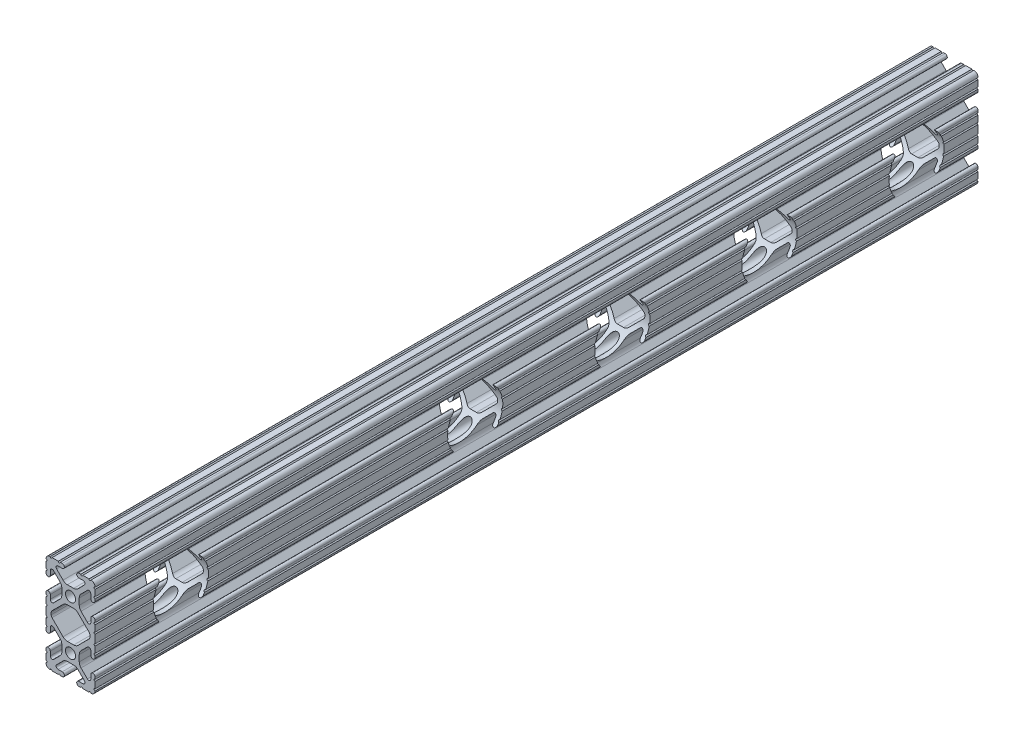
SolidWorks part; units mm, degrees
ref_plane "Front Plane" through (0, 0, 0) normal (0, 0, 1) x (1, 0, 0)
ref_plane "Top Plane" through (0, 0, 0) normal (0, 1, 0) x (1, 0, 0)
ref_plane "Right Plane" through (0, 0, 0) normal (1, 0, 0) x (0, 0, -1)
ref_plane "Plane1" through (0, 0, -889) normal (0, 0, -1) x (-1, 0, 0)
sketch "Sketch1" plane through (0, 0, -889) normal (0, 0, -1) x (-1, 0, 0)
  line L0 (10.033, 13.1521) -> (10.033, 12.2479)
  line L1 (9.5718, 11.1343) -> (3.8759, 5.4384)
  line L2 (1.6308, 4.5085) -> (-1.6308, 4.5085)
  line L3 (-3.8759, 5.4384) -> (-9.5718, 11.1343)
  line L4 (-10.033, 12.2479) -> (-10.033, 13.1521)
  line L5 (-9.5718, 14.2657) -> (-3.8759, 19.9616)
  line L6 (-1.6308, 20.8915) -> (1.6308, 20.8915)
  line L7 (3.8759, 19.9616) -> (9.5718, 14.2657)
  line L8 (9.5504, 38.1) -> (6.3246, 38.1)
  line L9 (5.3086, 38.1) -> (4.3023, 38.1)
  line L10 (4.3023, 35.8902) -> (6.4748, 35.8902)
  line L11 (7.1932, 34.1558) -> (3.8759, 30.8384)
  line L12 (1.6308, 29.9085) -> (-1.6308, 29.9085)
  line L13 (-3.8759, 30.8384) -> (-7.1932, 34.1558)
  line L14 (-6.4748, 35.8902) -> (-4.3023, 35.8902)
  line L15 (-4.3023, 38.1) -> (-5.3086, 38.1)
  line L16 (-6.3246, 38.1) -> (-9.5504, 38.1)
  line L17 (-12.7, 34.9504) -> (-12.7, 31.7246)
  line L18 (-12.7, 30.7086) -> (-12.7, 29.7023)
  line L19 (-10.4902, 29.7023) -> (-10.4902, 31.8748)
  line L20 (-8.7558, 32.5932) -> (-5.4384, 29.2759)
  line L21 (-4.5085, 27.0308) -> (-4.5085, 23.7692)
  line L22 (-5.4384, 21.5241) -> (-8.7558, 18.2068)
  line L23 (-10.4902, 18.9252) -> (-10.4902, 21.0977)
  line L24 (-12.7, 21.0977) -> (-12.7, 20.0914)
  line L25 (-12.7, 19.0754) -> (-12.7, 15.8496)
  line L26 (-12.7, 14.8336) -> (-12.7, 10.5664)
  line L27 (-12.7, 9.5504) -> (-12.7, 6.3246)
  line L28 (-12.7, 5.3086) -> (-12.7, 4.3023)
  line L29 (-10.4902, 4.3023) -> (-10.4902, 6.4748)
  line L30 (-8.7558, 7.1932) -> (-5.4384, 3.8759)
  line L31 (-4.5085, 1.6308) -> (-4.5085, -1.6308)
  line L32 (-5.4384, -3.8759) -> (-8.7558, -7.1932)
  line L33 (-10.4902, -6.4748) -> (-10.4902, -4.3023)
  line L34 (-12.7, -4.3023) -> (-12.7, -5.3086)
  line L35 (-12.7, -6.3246) -> (-12.7, -9.5504)
  line L36 (-9.5504, -12.7) -> (-6.3246, -12.7)
  line L37 (-5.3086, -12.7) -> (-4.3023, -12.7)
  line L38 (-4.3023, -10.4902) -> (-6.4748, -10.4902)
  line L39 (-7.1932, -8.7558) -> (-3.8759, -5.4384)
  line L40 (-1.6308, -4.5085) -> (1.6308, -4.5085)
  line L41 (3.8759, -5.4384) -> (7.1932, -8.7558)
  line L42 (6.4748, -10.4902) -> (4.3023, -10.4902)
  line L43 (4.3023, -12.7) -> (5.3086, -12.7)
  line L44 (6.3246, -12.7) -> (9.5504, -12.7)
  line L45 (12.7, -9.5504) -> (12.7, -6.3246)
  line L46 (12.7, -5.3086) -> (12.7, -4.3023)
  line L47 (10.4902, -4.3023) -> (10.4902, -6.4748)
  line L48 (8.7558, -7.1932) -> (5.4384, -3.8759)
  line L49 (4.5085, -1.6308) -> (4.5085, 1.6308)
  line L50 (5.4384, 3.8759) -> (8.7558, 7.1932)
  line L51 (10.4902, 6.4748) -> (10.4902, 4.3023)
  line L52 (12.7, 4.3023) -> (12.7, 5.3086)
  line L53 (12.7, 6.3246) -> (12.7, 9.5504)
  line L54 (12.7, 10.5664) -> (12.7, 14.8336)
  line L55 (12.7, 15.8496) -> (12.7, 19.0754)
  line L56 (12.7, 20.0914) -> (12.7, 21.0977)
  line L57 (10.4902, 21.0977) -> (10.4902, 18.9252)
  line L58 (8.7558, 18.2068) -> (5.4384, 21.5241)
  line L59 (4.5085, 23.7692) -> (4.5085, 27.0308)
  line L60 (5.4384, 29.2759) -> (8.7558, 32.5932)
  line L61 (10.4902, 31.8748) -> (10.4902, 29.7023)
  line L62 (12.7, 29.7023) -> (12.7, 30.7086)
  line L63 (12.7, 31.7246) -> (12.7, 34.9504)
  arc A0 (10.033, 12.2479) -> (9.5718, 11.1343) centre (8.4582, 12.2479) cw
  arc A1 (3.8759, 5.4384) -> (1.6308, 4.5085) centre (1.6308, 7.6835) cw
  arc A2 (-1.6308, 4.5085) -> (-3.8759, 5.4384) centre (-1.6308, 7.6835) cw
  arc A3 (-9.5718, 11.1343) -> (-10.033, 12.2479) centre (-8.4582, 12.2479) cw
  arc A4 (-10.033, 13.1521) -> (-9.5718, 14.2657) centre (-8.4582, 13.1521) cw
  arc A5 (-3.8759, 19.9616) -> (-1.6308, 20.8915) centre (-1.6308, 17.7165) cw
  arc A6 (1.6308, 20.8915) -> (3.8759, 19.9616) centre (1.6308, 17.7165) cw
  arc A7 (9.5718, 14.2657) -> (10.033, 13.1521) centre (8.4582, 13.1521) cw
  circle A8 centre (0, 25.4) radius 2.6035
  arc A9 (12.7, 35.9791) -> (10.5791, 38.1) centre (10.5918, 35.9918) ccw
  arc A10 (10.5791, 38.1) -> (9.5504, 38.1) centre (10.0647, 38.1063) cw
  arc A11 (6.3246, 38.1) -> (5.3086, 38.1) centre (5.8166, 38.1) cw
  arc A12 (4.3023, 38.1) -> (4.3023, 35.8902) centre (4.3023, 36.9951) ccw
  arc A13 (6.4748, 35.8902) -> (7.1932, 34.1558) centre (6.4748, 34.8742) cw
  arc A14 (3.8759, 30.8384) -> (1.6308, 29.9085) centre (1.6308, 33.0835) cw
  arc A15 (-1.6308, 29.9085) -> (-3.8759, 30.8384) centre (-1.6308, 33.0835) cw
  arc A16 (-7.1932, 34.1558) -> (-6.4748, 35.8902) centre (-6.4748, 34.8742) cw
  arc A17 (-4.3023, 35.8902) -> (-4.3023, 38.1) centre (-4.3023, 36.9951) ccw
  arc A18 (-5.3086, 38.1) -> (-6.3246, 38.1) centre (-5.8166, 38.1) cw
  arc A19 (-9.5504, 38.1) -> (-10.5791, 38.1) centre (-10.0647, 38.1063) cw
  arc A20 (-10.5791, 38.1) -> (-12.7, 35.9791) centre (-10.5918, 35.9918) ccw
  arc A21 (-12.7, 35.9791) -> (-12.7, 34.9504) centre (-12.7063, 35.4647) cw
  arc A22 (-12.7, 31.7246) -> (-12.7, 30.7086) centre (-12.7, 31.2166) cw
  arc A23 (-12.7, 29.7023) -> (-10.4902, 29.7023) centre (-11.5951, 29.7023) ccw
  arc A24 (-10.4902, 31.8748) -> (-8.7558, 32.5932) centre (-9.4742, 31.8748) cw
  arc A25 (-5.4384, 29.2759) -> (-4.5085, 27.0308) centre (-7.6835, 27.0308) cw
  arc A26 (-4.5085, 23.7692) -> (-5.4384, 21.5241) centre (-7.6835, 23.7692) cw
  arc A27 (-8.7558, 18.2068) -> (-10.4902, 18.9252) centre (-9.4742, 18.9252) cw
  arc A28 (-10.4902, 21.0977) -> (-12.7, 21.0977) centre (-11.5951, 21.0977) ccw
  arc A29 (-12.7, 20.0914) -> (-12.7, 19.0754) centre (-12.7, 19.5834) cw
  arc A30 (-12.7, 15.8496) -> (-12.7, 14.8336) centre (-12.7, 15.3416) cw
  arc A31 (-12.7, 10.5664) -> (-12.7, 9.5504) centre (-12.7, 10.0584) cw
  arc A32 (-12.7, 6.3246) -> (-12.7, 5.3086) centre (-12.7, 5.8166) cw
  arc A33 (-12.7, 4.3023) -> (-10.4902, 4.3023) centre (-11.5951, 4.3023) ccw
  arc A34 (-10.4902, 6.4748) -> (-8.7558, 7.1932) centre (-9.4742, 6.4748) cw
  arc A35 (-5.4384, 3.8759) -> (-4.5085, 1.6308) centre (-7.6835, 1.6308) cw
  arc A36 (-4.5085, -1.6308) -> (-5.4384, -3.8759) centre (-7.6835, -1.6308) cw
  arc A37 (-8.7558, -7.1932) -> (-10.4902, -6.4748) centre (-9.4742, -6.4748) cw
  arc A38 (-10.4902, -4.3023) -> (-12.7, -4.3023) centre (-11.5951, -4.3023) ccw
  arc A39 (-12.7, -5.3086) -> (-12.7, -6.3246) centre (-12.7, -5.8166) cw
  arc A40 (-12.7, -9.5504) -> (-12.7, -10.5791) centre (-12.7063, -10.0647) cw
  arc A41 (-12.7, -10.5791) -> (-10.5791, -12.7) centre (-10.5918, -10.5918) ccw
  arc A42 (-10.5791, -12.7) -> (-9.5504, -12.7) centre (-10.0647, -12.7063) cw
  arc A43 (-6.3246, -12.7) -> (-5.3086, -12.7) centre (-5.8166, -12.7) cw
  arc A44 (-4.3023, -12.7) -> (-4.3023, -10.4902) centre (-4.3023, -11.5951) ccw
  arc A45 (-6.4748, -10.4902) -> (-7.1932, -8.7558) centre (-6.4748, -9.4742) cw
  arc A46 (-3.8759, -5.4384) -> (-1.6308, -4.5085) centre (-1.6308, -7.6835) cw
  arc A47 (1.6308, -4.5085) -> (3.8759, -5.4384) centre (1.6308, -7.6835) cw
  arc A48 (7.1932, -8.7558) -> (6.4748, -10.4902) centre (6.4748, -9.4742) cw
  arc A49 (4.3023, -10.4902) -> (4.3023, -12.7) centre (4.3023, -11.5951) ccw
  arc A50 (5.3086, -12.7) -> (6.3246, -12.7) centre (5.8166, -12.7) cw
  arc A51 (9.5504, -12.7) -> (10.5791, -12.7) centre (10.0647, -12.7063) cw
  arc A52 (10.5791, -12.7) -> (12.7, -10.5791) centre (10.5918, -10.5918) ccw
  arc A53 (12.7, -10.5791) -> (12.7, -9.5504) centre (12.7063, -10.0647) cw
  arc A54 (12.7, -6.3246) -> (12.7, -5.3086) centre (12.7, -5.8166) cw
  arc A55 (12.7, -4.3023) -> (10.4902, -4.3023) centre (11.5951, -4.3023) ccw
  arc A56 (10.4902, -6.4748) -> (8.7558, -7.1932) centre (9.4742, -6.4748) cw
  arc A57 (5.4384, -3.8759) -> (4.5085, -1.6308) centre (7.6835, -1.6308) cw
  arc A58 (4.5085, 1.6308) -> (5.4384, 3.8759) centre (7.6835, 1.6308) cw
  arc A59 (8.7558, 7.1932) -> (10.4902, 6.4748) centre (9.4742, 6.4748) cw
  arc A60 (10.4902, 4.3023) -> (12.7, 4.3023) centre (11.5951, 4.3023) ccw
  arc A61 (12.7, 5.3086) -> (12.7, 6.3246) centre (12.7, 5.8166) cw
  arc A62 (12.7, 9.5504) -> (12.7, 10.5664) centre (12.7, 10.0584) cw
  arc A63 (12.7, 14.8336) -> (12.7, 15.8496) centre (12.7, 15.3416) cw
  arc A64 (12.7, 19.0754) -> (12.7, 20.0914) centre (12.7, 19.5834) cw
  arc A65 (12.7, 21.0977) -> (10.4902, 21.0977) centre (11.5951, 21.0977) ccw
  arc A66 (10.4902, 18.9252) -> (8.7558, 18.2068) centre (9.4742, 18.9252) cw
  arc A67 (5.4384, 21.5241) -> (4.5085, 23.7692) centre (7.6835, 23.7692) cw
  arc A68 (4.5085, 27.0308) -> (5.4384, 29.2759) centre (7.6835, 27.0308) cw
  arc A69 (8.7558, 32.5932) -> (10.4902, 31.8748) centre (9.4742, 31.8748) cw
  arc A70 (10.4902, 29.7023) -> (12.7, 29.7023) centre (11.5951, 29.7023) ccw
  arc A71 (12.7, 30.7086) -> (12.7, 31.7246) centre (12.7, 31.2166) cw
  arc A72 (12.7, 34.9504) -> (12.7, 35.9791) centre (12.7063, 35.4647) cw
  circle A73 centre (0, 0) radius 2.6035
extrude "Boss-Extrude1" add sketch "Sketch1" against normal blind 457.2
ref_plane "Plane2" through (0, 0, -622.2238) normal (0, 0, 1) x (1, 0, 0)
ref_plane "Plane3" through (0, 12.7, 0) normal (0, 1, 0) x (1, 0, 0)
sketch "Sketch2" plane through (12.7, 0, 0) normal (1, 0, 0) x (0, 0, -1)
  line L0 (431.8, 12.7) -> (889, 12.7) construction
  line L1 (431.8, 14.8336) -> (431.8, 10.5664) construction
  line L2 (889, 14.8336) -> (889, 10.5664) construction
  circle A0 centre (857.25, 12.7) radius 14.2875
  circle A1 centre (781.05, 12.7) radius 14.2875
  circle A2 centre (704.85, 12.7) radius 14.2875
  circle A3 centre (628.65, 12.7) radius 14.2875
  circle A4 centre (552.45, 12.7) radius 14.2875 [skipped]
  circle A5 centre (476.25, 12.7) radius 14.2875
  dimension "D1" = 28.575
  dimension "D2" = 31.75
  dimension "D3" = 6
extrude "Cut-Extrude1" cut sketch "Sketch2" against normal through all both and the other way through all
